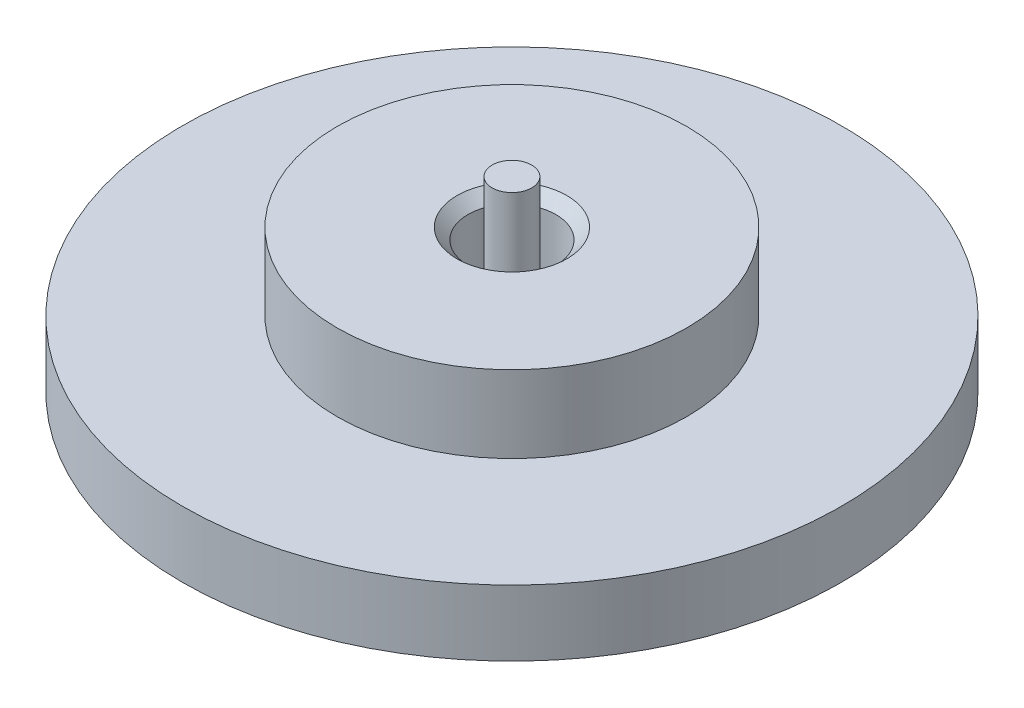
SolidWorks part; units mm, degrees
ref_plane "前视基准面" through (0, 0, 0) normal (0, 0, 1) x (1, 0, 0)
ref_plane "上视基准面" through (0, 0, 0) normal (0, 1, 0) x (1, 0, 0)
ref_plane "右视基准面" through (0, 0, 0) normal (1, 0, 0) x (0, 0, -1)
other "Configuration Table"
sketch "草图1" plane through (0, 0, 0) normal (0, 1, 0) x (1, 0, 0)
  circle A0 centre (0, 0) radius 15
  dimension "D1" = 30
extrude "凸台-拉伸1" add sketch "草图1" along normal blind 3
sketch "草图2" plane through (0, 3, 0) normal (0, 1, 0) x (1, 0, 0)
  circle A0 centre (0, 0) radius 7.95
  dimension "D1" = 15.9
extrude "凸台-拉伸2" add sketch "草图2" along normal blind 3.5
sketch "草图3" plane through (0, 6.5, 0) normal (0, 1, 0) x (1, 0, 0)
  circle A0 centre (0, 0) radius 0.9
  dimension "D1" = 1.8
extrude "凸台-拉伸3" add sketch "草图3" along normal blind 2
sketch "草图4" plane through (0, 6.5, 0) normal (0, 1, 0) x (1, 0, 0)
  circle A0 centre (0, 0) radius 2
  circle A1 centre (0, 0) radius 0.9 construction
  circle A2 centre (0, 0) radius 0.9
  dimension "D1" = 4
extrude "切除-拉伸1" cut sketch "草图4" against normal blind 3
chamfer "倒角1" distance 0.5 angle 45 1 edges at (0, 6.5, 2)
